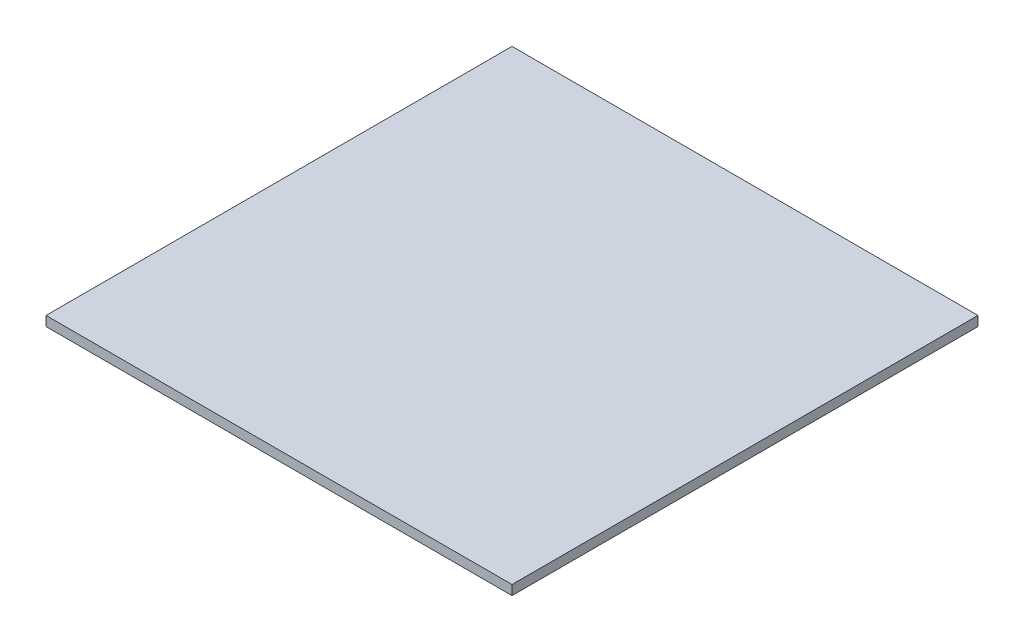
SolidWorks part; units mm, degrees
ref_plane "Front Plane" through (0, 0, 0) normal (0, 0, 1) x (1, 0, 0)
ref_plane "Top Plane" through (0, 0, 0) normal (0, 1, 0) x (1, 0, 0)
ref_plane "Right Plane" through (0, 0, 0) normal (1, 0, 0) x (0, 0, -1)
sketch "Sketch2" plane through (0, 0, 0) normal (0, 1, 0) x (1, 0, 0)
  circle A0 centre (0, 0) radius 60
  dimension "D1" = 120
extrude "Boss-Extrude1" add sketch "Sketch2" along normal blind 36
sketch "Sketch3" plane through (0, 36, 0) normal (0, 1, 0) x (1, 0, 0)
  line L1 (-145, 145) -> (145, 145)
  line L2 (-145, 145) -> (-145, -145)
  line L3 (-145, -145) -> (145, -145)
  line L4 (145, 145) -> (145, -145)
  point P4 (-145, 0)
  point P6 (0, -145)
  dimension "D1" = 290
extrude "Boss-Extrude2" add sketch "Sketch3" along normal blind 6
sketch "Sketch4" plane through (0, 0, 0) normal (0, -1, 0) x (1, 0, 0)
  line L1 (-166, 166) -> (166, 166)
  line L2 (-166, 166) -> (-166, -166)
  line L3 (-166, -166) -> (166, -166)
  line L4 (166, 166) -> (166, -166)
  point P4 (0, -166)
  point P5 (-166, 0)
  dimension "D1" = 332
